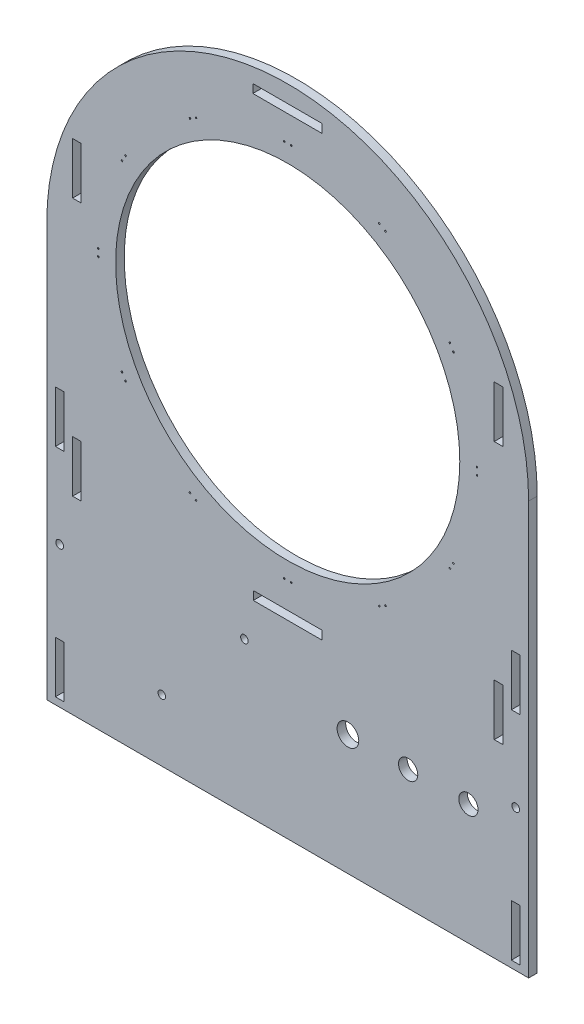
SolidWorks part; units mm, degrees
ref_plane "Front Plane" through (0, 0, 0) normal (0, 0, 1) x (1, 0, 0)
ref_plane "Top Plane" through (0, 0, 0) normal (0, 1, 0) x (1, 0, 0)
ref_plane "Right Plane" through (0, 0, 0) normal (1, 0, 0) x (0, 0, -1)
sketch "Sketch1" plane through (0, 0, 0) normal (0, 0, 1) x (1, 0, 0)
  line L0 (-88.9, 0) -> (-88.9, -152.4)
  line L1 (-88.9, -152.4) -> (88.9, -152.4)
  line L2 (88.9, -152.4) -> (88.9, 0)
  line L3 (0, 63.5) -> (0, 69.85) construction
  line L4 (1.3017, 69.85) -> (-1.3017, 69.85) construction
  line L5 (1.5684, 69.5833) -> (1.035, 70.1167) construction
  line L6 (-1.5684, 70.1167) -> (-1.035, 70.1167)
  line L7 (-1.5684, 70.1167) -> (-1.5684, 69.5833)
  line L8 (-1.5684, 69.5833) -> (-1.035, 69.5833)
  line L9 (-1.035, 70.1167) -> (-1.035, 69.5833)
  line L10 (-1.5684, 70.1167) -> (-1.035, 69.5833) construction
  line L11 (-1.5684, 69.5833) -> (-1.035, 70.1167) construction
  line L12 (1.5684, 70.1167) -> (1.035, 69.5833) construction
  line L13 (1.035, 70.1167) -> (1.035, 69.5833)
  line L14 (1.5684, 69.5833) -> (1.035, 69.5833)
  line L15 (1.5684, 70.1167) -> (1.5684, 69.5833)
  line L16 (1.5684, 70.1167) -> (1.035, 70.1167)
  line L17 (33.7, 61.5071) -> (34.162, 61.2404)
  line L18 (33.7, 61.5071) -> (33.4333, 61.0451)
  line L19 (33.4333, 61.0451) -> (33.8953, 60.7784)
  line L20 (34.162, 61.2404) -> (33.8953, 60.7784)
  line L21 (35.9547, 60.2053) -> (35.688, 59.7434)
  line L22 (36.15, 59.4767) -> (35.688, 59.7434)
  line L23 (36.4167, 59.9386) -> (36.15, 59.4767)
  line L24 (36.4167, 59.9386) -> (35.9547, 60.2053)
  line L25 (36.15, 59.4767) -> (35.9547, 60.2053) construction
  line L26 (33.7, 61.5071) -> (33.8953, 60.7784) construction
  line L27 (33.4333, 61.0451) -> (34.162, 61.2404) construction
  line L28 (36.4167, 59.9386) -> (35.688, 59.7434) construction
  line L29 (59.9386, 36.4167) -> (60.2053, 35.9547)
  line L30 (59.9386, 36.4167) -> (59.4767, 36.15)
  line L31 (59.4767, 36.15) -> (59.7434, 35.688)
  line L32 (60.2053, 35.9547) -> (59.7434, 35.688)
  line L33 (61.2404, 34.162) -> (60.7784, 33.8953)
  line L34 (61.0451, 33.4333) -> (60.7784, 33.8953)
  line L35 (61.5071, 33.7) -> (61.0451, 33.4333)
  line L36 (61.5071, 33.7) -> (61.2404, 34.162)
  line L37 (61.0451, 33.4333) -> (61.2404, 34.162) construction
  line L38 (59.9386, 36.4167) -> (59.7434, 35.688) construction
  line L39 (59.4767, 36.15) -> (60.2053, 35.9547) construction
  line L40 (61.5071, 33.7) -> (60.7784, 33.8953) construction
  line L41 (70.1167, 1.5685) -> (70.1167, 1.0351)
  line L42 (70.1167, 1.5685) -> (69.5833, 1.5685)
  line L43 (69.5833, 1.5685) -> (69.5833, 1.0351)
  line L44 (70.1167, 1.0351) -> (69.5833, 1.0351)
  line L45 (70.1167, -1.035) -> (69.5833, -1.035)
  line L46 (69.5833, -1.5684) -> (69.5833, -1.035)
  line L47 (70.1167, -1.5684) -> (69.5833, -1.5684)
  line L48 (70.1167, -1.5684) -> (70.1167, -1.035)
  line L49 (69.5833, -1.5684) -> (70.1167, -1.035) construction
  line L50 (70.1167, 1.5685) -> (69.5833, 1.0351) construction
  line L51 (69.5833, 1.5685) -> (70.1167, 1.0351) construction
  line L52 (70.1167, -1.5684) -> (69.5833, -1.035) construction
  line L53 (61.5071, -33.7) -> (61.2404, -34.162)
  line L54 (61.5071, -33.7) -> (61.0451, -33.4333)
  line L55 (61.0451, -33.4333) -> (60.7784, -33.8953)
  line L56 (61.2404, -34.162) -> (60.7784, -33.8953)
  line L57 (60.2053, -35.9547) -> (59.7434, -35.688)
  line L58 (59.4767, -36.15) -> (59.7434, -35.688)
  line L59 (59.9386, -36.4167) -> (59.4767, -36.15)
  line L60 (59.9386, -36.4167) -> (60.2053, -35.9547)
  line L61 (59.4767, -36.15) -> (60.2053, -35.9547) construction
  line L62 (61.5071, -33.7) -> (60.7784, -33.8953) construction
  line L63 (61.0451, -33.4333) -> (61.2404, -34.162) construction
  line L64 (59.9386, -36.4167) -> (59.7434, -35.688) construction
  line L65 (36.4167, -59.9386) -> (35.9547, -60.2053)
  line L66 (36.4167, -59.9386) -> (36.15, -59.4767)
  line L67 (36.15, -59.4767) -> (35.688, -59.7434)
  line L68 (35.9547, -60.2053) -> (35.688, -59.7434)
  line L69 (34.162, -61.2404) -> (33.8953, -60.7784)
  line L70 (33.4333, -61.0451) -> (33.8953, -60.7784)
  line L71 (33.7, -61.5071) -> (33.4333, -61.0451)
  line L72 (33.7, -61.5071) -> (34.162, -61.2404)
  line L73 (33.4333, -61.0451) -> (34.162, -61.2404) construction
  line L74 (36.4167, -59.9386) -> (35.688, -59.7434) construction
  line L75 (36.15, -59.4767) -> (35.9547, -60.2053) construction
  line L76 (33.7, -61.5071) -> (33.8953, -60.7784) construction
  line L77 (1.5685, -70.1167) -> (1.0351, -70.1167)
  line L78 (1.5685, -70.1167) -> (1.5685, -69.5833)
  line L79 (1.5685, -69.5833) -> (1.0351, -69.5833)
  line L80 (1.0351, -70.1167) -> (1.0351, -69.5833)
  line L81 (-1.035, -70.1167) -> (-1.035, -69.5833)
  line L82 (-1.5684, -69.5833) -> (-1.035, -69.5833)
  line L83 (-1.5684, -70.1167) -> (-1.5684, -69.5833)
  line L84 (-1.5684, -70.1167) -> (-1.035, -70.1167)
  line L85 (-1.5684, -69.5833) -> (-1.035, -70.1167) construction
  line L86 (1.5685, -70.1167) -> (1.0351, -69.5833) construction
  line L87 (1.5685, -69.5833) -> (1.0351, -70.1167) construction
  line L88 (-1.5684, -70.1167) -> (-1.035, -69.5833) construction
  line L89 (-33.7, -61.5071) -> (-34.162, -61.2404)
  line L90 (-33.7, -61.5071) -> (-33.4333, -61.0451)
  line L91 (-33.4333, -61.0451) -> (-33.8953, -60.7784)
  line L92 (-34.162, -61.2404) -> (-33.8953, -60.7784)
  line L93 (-35.9547, -60.2053) -> (-35.688, -59.7434)
  line L94 (-36.15, -59.4767) -> (-35.688, -59.7434)
  line L95 (-36.4167, -59.9386) -> (-36.15, -59.4767)
  line L96 (-36.4167, -59.9386) -> (-35.9547, -60.2053)
  line L97 (-36.15, -59.4767) -> (-35.9547, -60.2053) construction
  line L98 (-33.7, -61.5071) -> (-33.8953, -60.7784) construction
  line L99 (-33.4333, -61.0451) -> (-34.162, -61.2404) construction
  line L100 (-36.4167, -59.9386) -> (-35.688, -59.7434) construction
  line L101 (-59.9386, -36.4167) -> (-60.2053, -35.9547)
  line L102 (-59.9386, -36.4167) -> (-59.4767, -36.15)
  line L103 (-59.4767, -36.15) -> (-59.7434, -35.688)
  line L104 (-60.2053, -35.9547) -> (-59.7434, -35.688)
  line L105 (-61.2404, -34.162) -> (-60.7784, -33.8953)
  line L106 (-61.0451, -33.4333) -> (-60.7784, -33.8953)
  line L107 (-61.5071, -33.7) -> (-61.0451, -33.4333)
  line L108 (-61.5071, -33.7) -> (-61.2404, -34.162)
  line L109 (-61.0451, -33.4333) -> (-61.2404, -34.162) construction
  line L110 (-59.9386, -36.4167) -> (-59.7434, -35.688) construction
  line L111 (-59.4767, -36.15) -> (-60.2053, -35.9547) construction
  line L112 (-61.5071, -33.7) -> (-60.7784, -33.8953) construction
  line L113 (-70.1167, -1.5685) -> (-70.1167, -1.0351)
  line L114 (-70.1167, -1.5685) -> (-69.5833, -1.5685)
  line L115 (-69.5833, -1.5685) -> (-69.5833, -1.0351)
  line L116 (-70.1167, -1.0351) -> (-69.5833, -1.0351)
  line L117 (-70.1167, 1.035) -> (-69.5833, 1.035)
  line L118 (-69.5833, 1.5684) -> (-69.5833, 1.035)
  line L119 (-70.1167, 1.5684) -> (-69.5833, 1.5684)
  line L120 (-70.1167, 1.5684) -> (-70.1167, 1.035)
  line L121 (-69.5833, 1.5684) -> (-70.1167, 1.035) construction
  line L122 (-70.1167, -1.5685) -> (-69.5833, -1.0351) construction
  line L123 (-69.5833, -1.5685) -> (-70.1167, -1.0351) construction
  line L124 (-70.1167, 1.5684) -> (-69.5833, 1.035) construction
  line L125 (-61.5071, 33.7) -> (-61.2404, 34.162)
  line L126 (-61.5071, 33.7) -> (-61.0451, 33.4333)
  line L127 (-61.0451, 33.4333) -> (-60.7784, 33.8953)
  line L128 (-61.2404, 34.162) -> (-60.7784, 33.8953)
  line L129 (-60.2053, 35.9547) -> (-59.7434, 35.688)
  line L130 (-59.4767, 36.15) -> (-59.7434, 35.688)
  line L131 (-59.9386, 36.4167) -> (-59.4767, 36.15)
  line L132 (-59.9386, 36.4167) -> (-60.2053, 35.9547)
  line L133 (-59.4767, 36.15) -> (-60.2053, 35.9547) construction
  line L134 (-61.5071, 33.7) -> (-60.7784, 33.8953) construction
  line L135 (-61.0451, 33.4333) -> (-61.2404, 34.162) construction
  line L136 (-59.9386, 36.4167) -> (-59.7434, 35.688) construction
  line L137 (-36.4167, 59.9386) -> (-35.9547, 60.2053)
  line L138 (-36.4167, 59.9386) -> (-36.15, 59.4767)
  line L139 (-36.15, 59.4767) -> (-35.688, 59.7434)
  line L140 (-35.9547, 60.2053) -> (-35.688, 59.7434)
  line L141 (-34.162, 61.2404) -> (-33.8953, 60.7784)
  line L142 (-33.4333, 61.0451) -> (-33.8953, 60.7784)
  line L143 (-33.7, 61.5071) -> (-33.4333, 61.0451)
  line L144 (-33.7, 61.5071) -> (-34.162, 61.2404)
  line L145 (-33.4333, 61.0451) -> (-34.162, 61.2404) construction
  line L146 (-36.4167, 59.9386) -> (-35.688, 59.7434) construction
  line L147 (-36.15, 59.4767) -> (-35.9547, 60.2053) construction
  line L148 (-33.7, 61.5071) -> (-33.8953, 60.7784) construction
  line L149 (-79.375, 31.7348) -> (-76.2, 31.7348) construction
  line L150 (-76.2, 31.7348) -> (-79.375, 31.7348)
  line L151 (-76.2, 31.7348) -> (-76.2, 12.6848)
  line L152 (-76.2, 12.6848) -> (-79.375, 12.6848)
  line L153 (-79.375, 31.7348) -> (-79.375, 12.6848)
  line L154 (-76.2, 31.7348) -> (-76.2, 12.6848) construction
  line L155 (0, -152.4) -> (0, 0) construction
  line L156 (-76.2, -63.5152) -> (-79.375, -63.5152)
  line L157 (-76.2, -63.5152) -> (-76.2, -82.5652)
  line L158 (-76.2, -82.5652) -> (-79.375, -82.5652)
  line L159 (-79.375, -63.5152) -> (-79.375, -82.5652)
  line L160 (-82.55, -130.81) -> (-85.725, -130.81)
  line L161 (-82.55, -130.81) -> (-82.55, -149.86)
  line L162 (-82.55, -149.86) -> (-85.725, -149.86)
  line L163 (-85.725, -130.81) -> (-85.725, -149.86)
  line L164 (-82.55, -50.8) -> (-85.725, -50.8)
  line L165 (-82.55, -50.8) -> (-82.55, -69.85)
  line L166 (-82.55, -69.85) -> (-85.725, -69.85)
  line L167 (-85.725, -50.8) -> (-85.725, -69.85)
  line L168 (85.725, -130.81) -> (85.725, -149.86)
  line L169 (82.55, -149.86) -> (85.725, -149.86)
  line L170 (82.55, -130.81) -> (82.55, -149.86)
  line L171 (82.55, -130.81) -> (85.725, -130.81)
  line L172 (79.375, 31.7348) -> (79.375, 12.6848)
  line L173 (76.2, 12.6848) -> (79.375, 12.6848)
  line L174 (76.2, 31.7348) -> (76.2, 12.6848)
  line L175 (76.2, 31.7348) -> (79.375, 31.7348)
  line L176 (85.725, -50.8) -> (85.725, -69.85)
  line L177 (82.55, -69.85) -> (85.725, -69.85)
  line L178 (82.55, -50.8) -> (82.55, -69.85)
  line L179 (82.55, -50.8) -> (85.725, -50.8)
  line L180 (79.375, -63.5152) -> (79.375, -82.5652)
  line L181 (76.2, -82.5652) -> (79.375, -82.5652)
  line L182 (76.2, -63.5152) -> (76.2, -82.5652)
  line L183 (76.2, -63.5152) -> (79.375, -63.5152)
  line L184 (12.7, 79.375) -> (12.7, 82.55)
  line L185 (12.7, 79.375) -> (-12.8563, 79.375)
  line L186 (12.7, 82.55) -> (-12.8563, 82.55)
  line L187 (-12.8563, 79.375) -> (-12.8563, 82.55)
  line L188 (12.7, -82.55) -> (12.7, -79.375)
  line L189 (12.7, -82.55) -> (-12.7, -82.55)
  line L190 (12.7, -79.375) -> (-12.7, -79.375)
  line L191 (-12.7, -82.55) -> (-12.7, -79.375)
  line L192 (-12.7, -82.55) -> (-12.7, -79.375) construction
  line L193 (-85.725, -98.806) -> (-82.55, -98.806) construction
  line L194 (-82.55, -97.155) -> (-82.55, -103.505) construction
  circle A0 centre (0, 0) radius 63.5
  circle A1 centre (-84.1375, -100.33) radius 1.4224
  arc A2 (88.9, 0) -> (-88.9, 0) centre (0, 0) ccw
  circle A3 centre (84.1375, -100.33) radius 1.4224
  circle A4 centre (22.225, -107.95) radius 4
  circle A5 centre (44.45, -107.95) radius 3.55
  circle A6 centre (66.675, -107.95) radius 3.55
  circle A9 centre (-15.9776, -96.52) radius 1.397
  circle A10 centre (-15.9776, -96.52) radius 1.397 construction
  circle A11 centre (-46.4576, -129.54) radius 1.397
  circle A12 centre (-46.4576, -129.54) radius 1.397 construction
  point P11 (0, 69.85)
  point P171 (-84.1375, -98.806)
  point P174 (-82.55, -100.33)
  dimension "D1" = 127
  dimension "D2" = 88.9
  dimension "D7" = 0.5334
  dimension "D8" = 2.8448
  dimension "D9" = 8
  dimension "D12" = 7.1
  dimension "D13" = 7.1
  dimension "D3" = 177.8
  dimension "D4" = 152.4
  dimension "D5" = 6.35
  dimension "D6" = 2.6035
  dimension "D10" = 66.675
  dimension "D11" = 44.45
  dimension "D14" = 44.45
  dimension "D15" = 22.225
extrude "Boss-Extrude1" add sketch "Sketch1" along normal blind 3.175
ref_plane "Plane1" through (88.9, -152.4, 0) normal (1, 0, 0) x (0, 0, -1)
